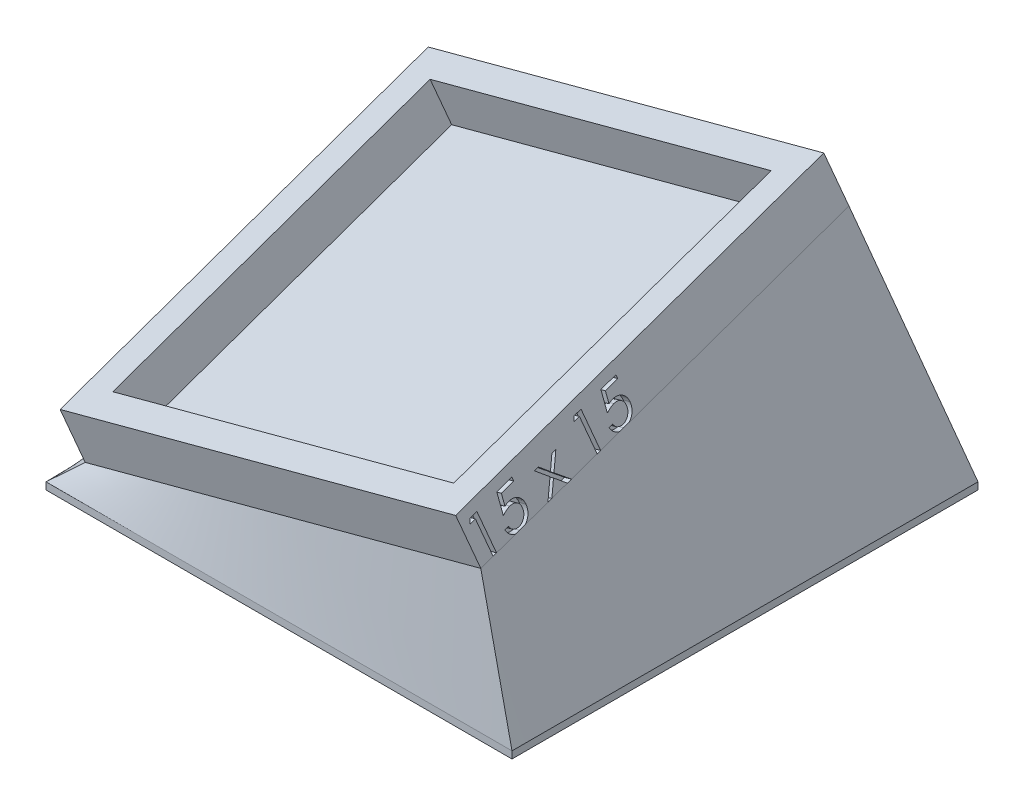
SolidWorks part; units mm, degrees
ref_plane "Front Plane" through (0, 0, 0) normal (0, 0, 1) x (1, 0, 0)
ref_plane "Top Plane" through (0, 0, 0) normal (0, 1, 0) x (1, 0, 0)
ref_plane "Right Plane" through (0, 0, 0) normal (1, 0, 0) x (0, 0, -1)
sketch "Sketch1" plane through (0, 0, 0) normal (0, 1, 0) x (1, 0, 0)
  line L1 (-22.2888, 13.0013) -> (14.5412, 13.0013)
  line L2 (-22.2888, 13.0013) -> (-22.2888, -23.8287)
  line L3 (-22.2888, -23.8287) -> (14.5412, -23.8287)
  line L4 (14.5412, 13.0013) -> (14.5412, -23.8287)
  dimension "D1" = 36.83
  dimension "D2" = 36.83
extrude "Boss-Extrude1" add sketch "Sketch1" along normal blind 0.635
sketch "Sketch2" plane through (0, 0.635, 0) normal (0, 1, 0) x (1, 0, 0)
  line L0 (14.5412, 13.0013) -> (-22.2888, 13.0013) construction
  line L1 (-19.7488, 10.4613) -> (12.0012, 10.4613)
  line L2 (-19.7488, 10.4613) -> (-19.7488, -21.2887)
  line L3 (-19.7488, -21.2887) -> (12.0012, -21.2887)
  line L4 (12.0012, 10.4613) -> (12.0012, -21.2887)
  line L5 (-22.2888, 13.0013) -> (-22.2888, -23.8287) construction
  line L7 (-22.2888, 13.0013) -> (14.5412, 13.0013)
  line L8 (-22.2888, 13.0013) -> (-22.2888, -23.8287)
  line L9 (-22.2888, -23.8287) -> (14.5412, -23.8287)
  line L10 (14.5412, 13.0013) -> (14.5412, -23.8287)
  dimension "D1" = 31.75
  dimension "D2" = 31.75
  dimension "D3" = 2.54
  dimension "D4" = 2.54
extrude "Boss-Extrude2" add sketch "Sketch2" along normal blind 3.81 contours L8 L7 L10 L9 | L2 L1 L4 L3
move or copy body "Body-Move/Copy1" bodies to move or copy 102 copy no translate (0, 12.7, 0)
sketch "Sketch3" plane through (0, 0, 0) normal (0, 1, 0) x (1, 0, 0)
  line L0 (-22.2888, 13.0013) -> (-22.2888, -23.8287) construction
  line L1 (-24.8288, 15.5413) -> (17.0812, 15.5413)
  line L2 (-24.8288, 15.5413) -> (-24.8288, -26.3687)
  line L3 (-24.8288, -26.3687) -> (17.0812, -26.3687)
  line L4 (17.0812, 15.5413) -> (17.0812, -26.3687)
  line L5 (-22.2888, -23.8287) -> (14.5412, -23.8287) construction
  dimension "D1" = 41.91
  dimension "D2" = 41.91
  dimension "D3" = 2.54
  dimension "D4" = 2.54
extrude "Boss-Extrude3" add sketch "Sketch3" along normal blind 0.635 separate body
move or copy body "Body-Move/Copy2" bodies to move or copy 103 copy no rotation origin (-4.9479, 4.6211, 4.3395) rotation axis (0.7041, 0.0927, 0.7041) rotation angle 21.183
loft "Loft1" add section face at (-5.8581, 12.1683, 7.4681) section face at (-3.8738, 0.635, 5.4137)
sketch "Sketch5" plane through (15.3639, 4.1167, 0) normal (0.9659, 0.2588, 0) x (0, 0, -1)
  text T0 "15 x 15"
extrude "Cut-Extrude2" cut sketch "Sketch5" against normal blind 0.635
